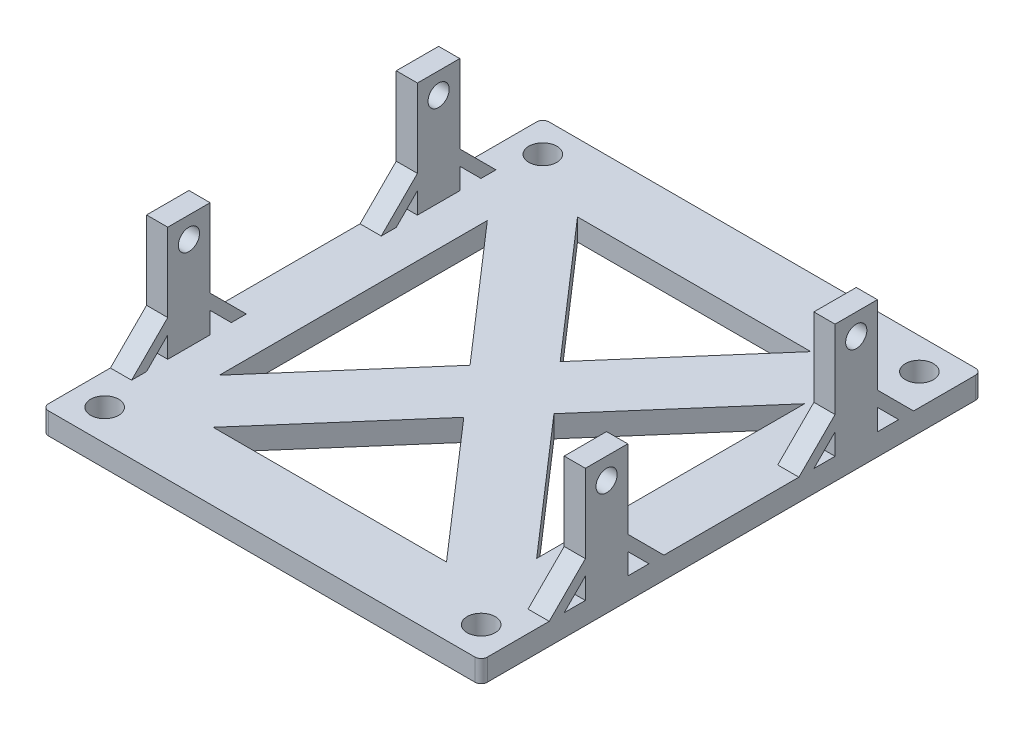
SolidWorks part; units mm, degrees
ref_plane "Front Plane" through (0, 0, 0) normal (0, 0, 1) x (1, 0, 0)
ref_plane "Top Plane" through (0, 0, 0) normal (0, 1, 0) x (1, 0, 0)
ref_plane "Right Plane" through (0, 0, 0) normal (1, 0, 0) x (0, 0, -1)
sketch "Sketch1" plane through (0, 0, 0) normal (0, 1, 0) x (1, 0, 0)
  line L0 (-31.8135, 27.2502) -> (-31.8135, -27.2502) construction
  line L1 (35.2135, 30.1625) -> (-35.2135, 30.1625)
  line L2 (35.2135, 30.1625) -> (35.2135, -30.1625)
  line L3 (35.2135, -30.1625) -> (-35.2135, -30.1625)
  line L4 (-35.2135, 30.1625) -> (-35.2135, -30.1625)
  line L5 (35.2135, 30.1625) -> (-35.2135, -30.1625) construction
  line L6 (35.2135, -30.1625) -> (-35.2135, 30.1625) construction
  line L8 (31.8135, 27.2502) -> (31.8135, -27.2502) construction
  point P0 (0, 0)
  dimension "D1" = 60.325
  dimension "D2" = 63.627
  dimension "D3" = 3.4
  dimension "D4" = 3.4
extrude "Boss-Extrude1" add sketch "Sketch1" along normal blind 3.5
sketch "Sketch4" plane through (-35.2135, 0, 0) normal (-1, 0, 0) x (0, 0, 1)
  line L0 (-29.2398, 3.5) -> (-23.4356, 9.3042)
  line L1 (-30.1625, 3.5) -> (30.1625, 3.5) construction
  line L2 (-29.2398, 3.5) -> (-26.8356, 3.5)
  line L3 (-26.8356, 3.5) -> (-23.4356, 6.9)
  line L4 (-23.4356, 9.3042) -> (-23.4356, 21.8688)
  line L5 (-23.4356, 21.8688) -> (-16.6356, 21.8688)
  line L6 (-20.0356, 21.8688) -> (-20.0356, 3.5) construction
  line L7 (-23.4356, 6.9) -> (-23.4356, 3.5)
  line L8 (-10.8315, 3.5) -> (-16.6356, 9.3042)
  line L9 (-10.8315, 3.5) -> (-13.2356, 3.5)
  line L10 (-23.4356, 3.5) -> (-16.6356, 3.5)
  line L11 (-13.2356, 3.5) -> (-16.6356, 6.9)
  line L12 (-16.6356, 6.9) -> (-16.6356, 3.5)
  line L13 (-30.1625, 0) -> (30.1625, 0) construction
  line L14 (-30.1625, 3.5) -> (-30.1625, 0) construction
  line L15 (-16.6356, 9.3042) -> (-16.6356, 21.8688)
  circle A0 centre (-20.0356, 18.4688) radius 1.7
  dimension "D4" = 3.4
  dimension "D5" = 3.4
  dimension "D6" = 20.1688
  dimension "D1" = 11.8269
  dimension "D2" = 45
  dimension "D3" = 3.4
  dimension "D7" = 1.7
  dimension "D8" = 3.4
extrude "Boss-Extrude2" add sketch "Sketch4" against normal blind 3.4
ref_plane "Plane12" through (0, 0, 0) normal (1, 0, 0) x (0, 0, -1)
ref_plane "Plane13" through (0, 0, 0) normal (0, 0, -1) x (-1, 0, 0)
mirror "Mirror1" about plane through (0, 0, 0) normal (1, 0, 0) of "Boss-Extrude2" second plane through (0, 0, 0) second plane normal (0, 0, -1)
sketch "Sketch6" plane through (0, 3.5, 0) normal (0, 1, 0) x (1, 0, 0)
  line L0 (35.2135, -10.8315) -> (35.2135, 10.8315) construction
  line L1 (-35.2135, 30.1625) -> (35.2135, 30.1625)
  line L2 (-35.2135, 30.1625) -> (-35.2135, 40.1625)
  line L3 (-35.2135, 40.1625) -> (35.2135, 40.1625)
  line L4 (35.2135, 30.1625) -> (35.2135, 40.1625)
  line L5 (0, 30.1625) -> (0, 40.1625) construction
  circle A0 centre (-30.2135, 35.1625) radius 2.25
  circle A1 centre (30.2135, 35.1625) radius 2.25
  dimension "D2" = 5
  dimension "D3" = 5
  dimension "D4" = 4.5
  dimension "D1" = 10
extrude "Boss-Extrude3" add sketch "Sketch6" against normal blind 3.5
ref_plane "Plane9" through (0, 0, 0) normal (0, 0, 1) x (1, 0, 0)
mirror "Mirror2" about plane through (0, 0, 0) normal (0, 0, 1) of "Boss-Extrude3"
fillet "Fillet1" radius 1 4 edges at (-35.2135, 1.75, 40.1625) (35.2135, 1.75, 40.1625) (35.2135, 1.75, -40.1625) (-35.2135, 1.75, -40.1625)
sketch "Sketch7" plane through (0, 3.5, 0) normal (0, 1, 0) x (1, 0, 0)
  line L0 (18.7272, 29.2398) -> (0, 7.7353)
  line L1 (25.4635, 29.2398) -> (-25.4635, 29.2398)
  line L2 (25.4635, 29.2398) -> (25.4635, -29.2398)
  line L3 (25.4635, -29.2398) -> (-25.4635, -29.2398)
  line L4 (-25.4635, 29.2398) -> (-25.4635, -29.2398)
  line L5 (25.4635, 29.2398) -> (-25.4635, -29.2398) construction
  line L6 (25.4635, -29.2398) -> (-25.4635, 29.2398) construction
  line L7 (25.4635, -21.5045) -> (6.7363, 0)
  line L8 (25.4635, 21.5045) -> (6.7363, 0)
  line L9 (18.7272, -29.2398) -> (0, -7.7353)
  line L10 (-31.8135, 29.2398) -> (-35.2135, 29.2398) construction
  line L11 (-31.8135, 23.4356) -> (-31.8135, 29.2398) construction
  line L12 (21.6325, -32.576) -> (-29.2945, 25.9036) construction
  line L13 (29.2945, -25.9036) -> (-21.6325, 32.576) construction
  line L14 (21.6325, 32.576) -> (-29.2945, -25.9036) construction
  line L15 (29.2945, 25.9036) -> (-21.6325, -32.576) construction
  line L16 (-6.7363, 0) -> (-25.4635, -21.5045)
  line L17 (0, 7.7353) -> (-18.7272, 29.2398)
  line L18 (0, -7.7353) -> (-18.7272, -29.2398)
  line L19 (-6.7363, 0) -> (-25.4635, 21.5045)
  point P0 (0, 0)
  point P14 (-22.699, 27.2941)
  point P19 (-31.8135, 26.3377)
  point P20 (-26.2135, 21.6752)
  point P23 (-26.2135, 21.6296)
  point P24 (-19.2679, 29.2398)
  point P27 (19.3193, 29.2398)
  point P29 (26.2135, 21.6296)
  point P31 (19.3909, -29.2398)
  point P32 (26.2135, -21.5925)
  point P33 (-22.431, -32.6308)
  point P34 (-22.431, -32.6308)
  point P35 (0, 0)
  point P36 (-29.996, -25.8488)
  point P37 (-26.2135, -29.2398)
  point P38 (0, 0)
  point P39 (-29.996, -25.8488)
  dimension "D1" = 5.08
  dimension "D2" = 5.08
  dimension "D3" = 6.35
extrude "Cut-Extrude3" cut sketch "Sketch7" against normal through all both and the other way through all contours L17 L0 L1 | L2 L8 L7 | L9 L18 L3 | L16 L19 L4
